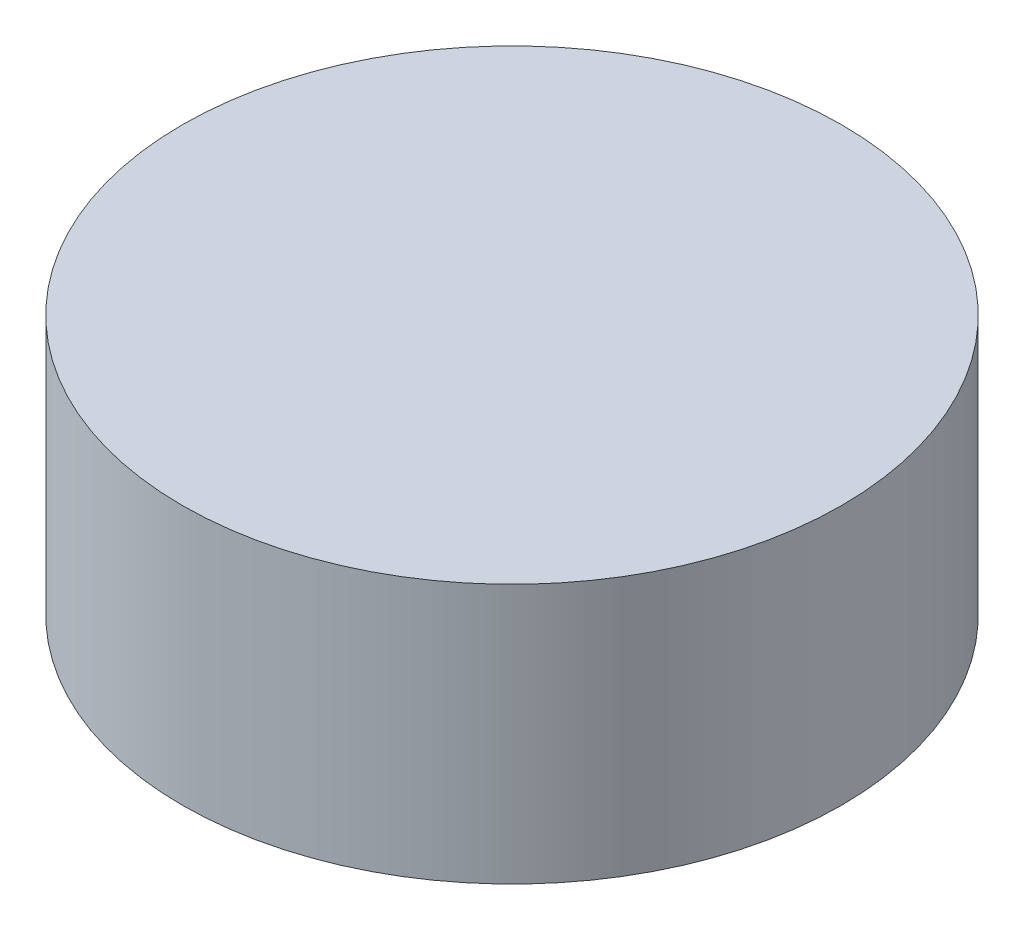
SolidWorks part; units mm, degrees
ref_plane "Front Plane" through (0, 0, 0) normal (0, 0, 1) x (1, 0, 0)
ref_plane "Top Plane" through (0, 0, 0) normal (0, 1, 0) x (1, 0, 0)
ref_plane "Right Plane" through (0, 0, 0) normal (1, 0, 0) x (0, 0, -1)
sketch "Sketch1" plane through (0, 0, 0) normal (0, 1, 0) x (1, 0, 0)
  circle A0 centre (0, 0) radius 12.7
  dimension "D1" = 25.4
extrude "Boss-Extrude1" add sketch "Sketch1" along normal blind 10
